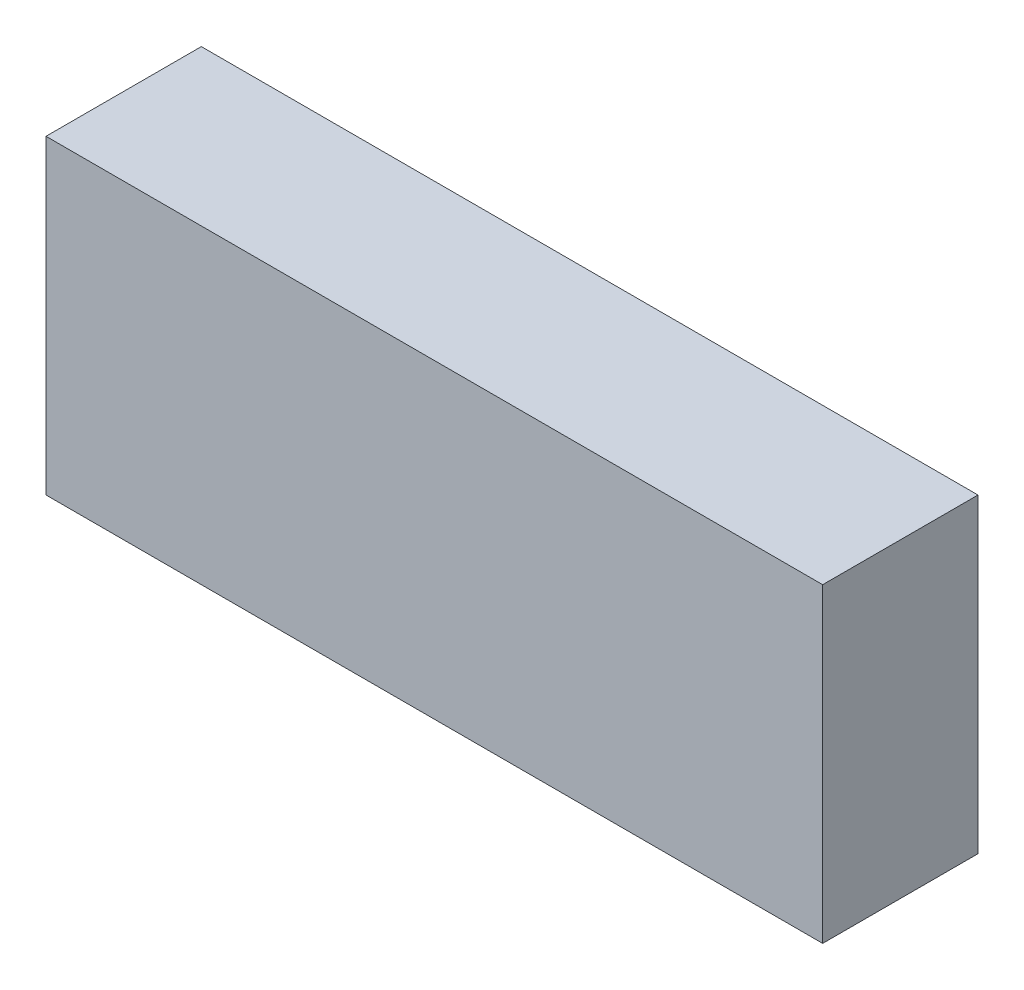
SolidWorks part; units mm, degrees
material "C (Grafite)"
ref_plane "Plano frontal" through (0, 0, 0) normal (0, 0, 1) x (1, 0, 0)
ref_plane "Plano superior" through (0, 0, 0) normal (0, 1, 0) x (1, 0, 0)
ref_plane "Plano direito" through (0, 0, 0) normal (1, 0, 0) x (0, 0, -1)
sketch "Esboço1" plane through (0, 0, 0) normal (0, 0, 1) x (1, 0, 0)
  line L1 (-25, 10) -> (25, 10)
  line L2 (-25, 10) -> (-25, -10)
  line L3 (-25, -10) -> (25, -10)
  line L4 (25, 10) -> (25, -10)
  line L5 (-25, 10) -> (25, -10) construction
  line L6 (-25, -10) -> (25, 10) construction
  point P0 (0, 0)
  dimension "D1" = 50
  dimension "D2" = 20
extrude "Ressalto-extrusão1" add sketch "Esboço1" along normal blind 10
